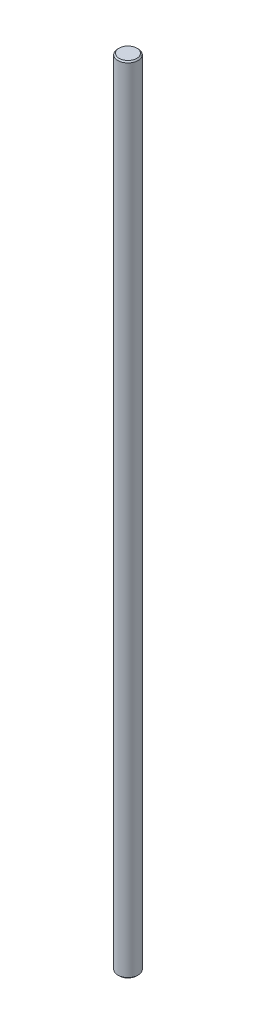
SolidWorks part; units mm, degrees
ref_plane "Front Plane" through (0, 0, 0) normal (0, 0, 1) x (1, 0, 0)
ref_plane "Top Plane" through (0, 0, 0) normal (0, 1, 0) x (1, 0, 0)
ref_plane "Right Plane" through (0, 0, 0) normal (1, 0, 0) x (0, 0, -1)
sketch "Sketch1" plane through (0, 0, 0) normal (0, 1, 0) x (1, 0, 0)
  circle A0 centre (0, 0) radius 4
  dimension "D1" = 8
extrude "Boss-Extrude1" add sketch "Sketch1" along normal mid plane 314
chamfer "Chamfer1" distance 0.5 angle 45 2 edges at (0, -157, 4) (0, 157, 4)
